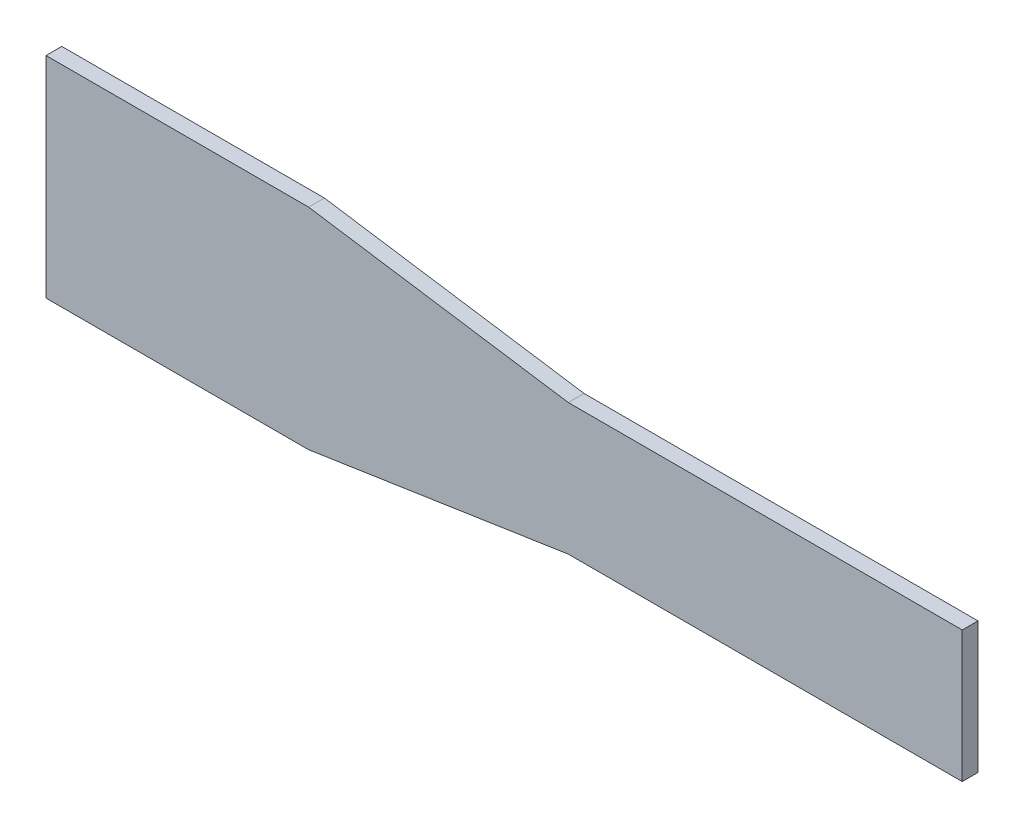
SolidWorks part; units mm, degrees
ref_plane "Plan de face" through (0, 0, 0) normal (0, 0, 1) x (1, 0, 0)
ref_plane "Plan de dessus" through (0, 0, 0) normal (0, 1, 0) x (1, 0, 0)
ref_plane "Plan de droite" through (0, 0, 0) normal (1, 0, 0) x (0, 0, -1)
sketch "Esquisse1" plane through (0, 0, 0) normal (0, 0, 1) x (1, 0, 0)
  line L0 (0, 12.5) -> (-49.4343, 20)
  line L1 (-75, 12.5) -> (75, 12.5) construction
  line L2 (-75, 12.5) -> (-75, -12.5) construction
  line L3 (-75, -12.5) -> (75, -12.5) construction
  line L4 (75, 12.5) -> (75, -12.5)
  line L5 (-75, 12.5) -> (75, -12.5) construction
  line L6 (-75, -12.5) -> (75, 12.5) construction
  line L8 (-49.4343, -20) -> (0, -12.5)
  line L9 (0, 12.5) -> (0, -12.5) construction
  line L10 (0, 12.5) -> (75, 12.5)
  line L11 (0, -12.5) -> (75, -12.5)
  line L12 (-49.4343, 20) -> (-99.4343, 20)
  line L13 (-99.4343, 20) -> (-99.4343, -20)
  line L14 (-99.4343, -20) -> (-49.4343, -20)
  point P0 (0, 0)
  dimension "D1" = 25
  dimension "D2" = 150
  dimension "D3" = 40
  dimension "D4" = 50
  dimension "D5" = 50
  dimension "D6" = 7.5
extrude "Boss.-Extru.1" add sketch "Esquisse1" along normal blind 3
